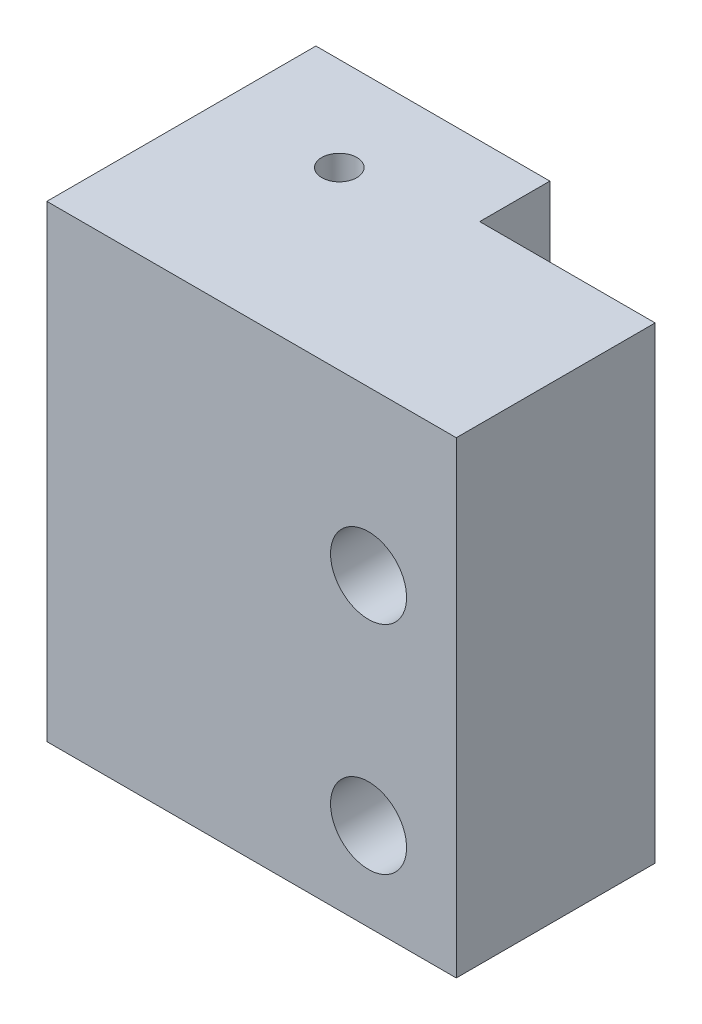
SolidWorks part; units mm, degrees
ref_plane "Front Plane" through (0, 0, 0) normal (0, 0, 1) x (1, 0, 0)
ref_plane "Top Plane" through (0, 0, 0) normal (0, 1, 0) x (1, 0, 0)
ref_plane "Right Plane" through (0, 0, 0) normal (1, 0, 0) x (0, 0, -1)
sketch "Sketch1" plane through (0, 0, 0) normal (0, 1, 0) x (1, 0, 0)
  line L5 (-10, -5.2575) -> (-10, 0.7425)
  line L6 (-10, 0.7425) -> (10, 0.7425)
  line L9 (25, -5.2575) -> (25, -22.2575)
  line L10 (0, -22.2575) -> (0, 0.7425) construction
  line L11 (-10, -5.2575) -> (-10, -22.2575)
  line L12 (10, 0.7425) -> (10, -5.2575)
  line L13 (10, -5.2575) -> (25, -5.2575)
  line L14 (-10, -22.2575) -> (25, -22.2575)
  point P2 (0, 0)
  dimension "D5" = 17
  dimension "D6" = 15
extrude "Boss-Extrude2" add sketch "Sketch1" along normal blind 40
sketch "Sketch3" plane through (0, 0, 0) normal (0, -1, 0) x (1, 0, 0)
  line L0 (0, -0.7425) -> (0, 22.2575) construction
  line L1 (10, -0.7425) -> (-10, -0.7425) construction
  circle A0 centre (0, 7.2575) radius 4.05
  dimension "D1" = 8.1
  dimension "D2" = 8
extrude "Cut-Extrude1" cut sketch "Sketch3" against normal blind 35
sketch "Sketch4" plane through (0, 0, 5.2575) normal (0, 0, -1) x (-1, 0, 0)
  line L0 (-25, 20) -> (-10, 20) construction
  line L1 (-25, 40) -> (-25, 0) construction
  line L2 (-10, 40) -> (-10, 0) construction
  line L3 (-17.5, 40) -> (-17.5, 0) construction
  line L4 (-25, 40) -> (-10, 40) construction
  line L5 (-25, 0) -> (-10, 0) construction
  circle A0 centre (-17.5, 26.0458) radius 3.25
  circle A2 centre (-17.5, 7.5353) radius 3.25
  dimension "D1" = 6.5
  dimension "D2" = 6.5
extrude "Cut-Extrude2" cut sketch "Sketch4" against normal up to next
sketch "Sketch5" plane through (0, 0, 0) normal (0, -1, 0) x (1, 0, 0)
  line L0 (0, -0.7425) -> (0, 22.2575) construction
  line L1 (10, -0.7425) -> (-10, -0.7425) construction
  line L2 (-10, 22.2575) -> (25, 22.2575) construction
sketch "Sketch6" plane through (0, 35, 0) normal (0, -1, 0) x (1, 0, 0)
  circle A0 centre (0, 7.2575) radius 1.5
  dimension "D1" = 3
extrude "Cut-Extrude3" cut sketch "Sketch6" against normal blind 10
